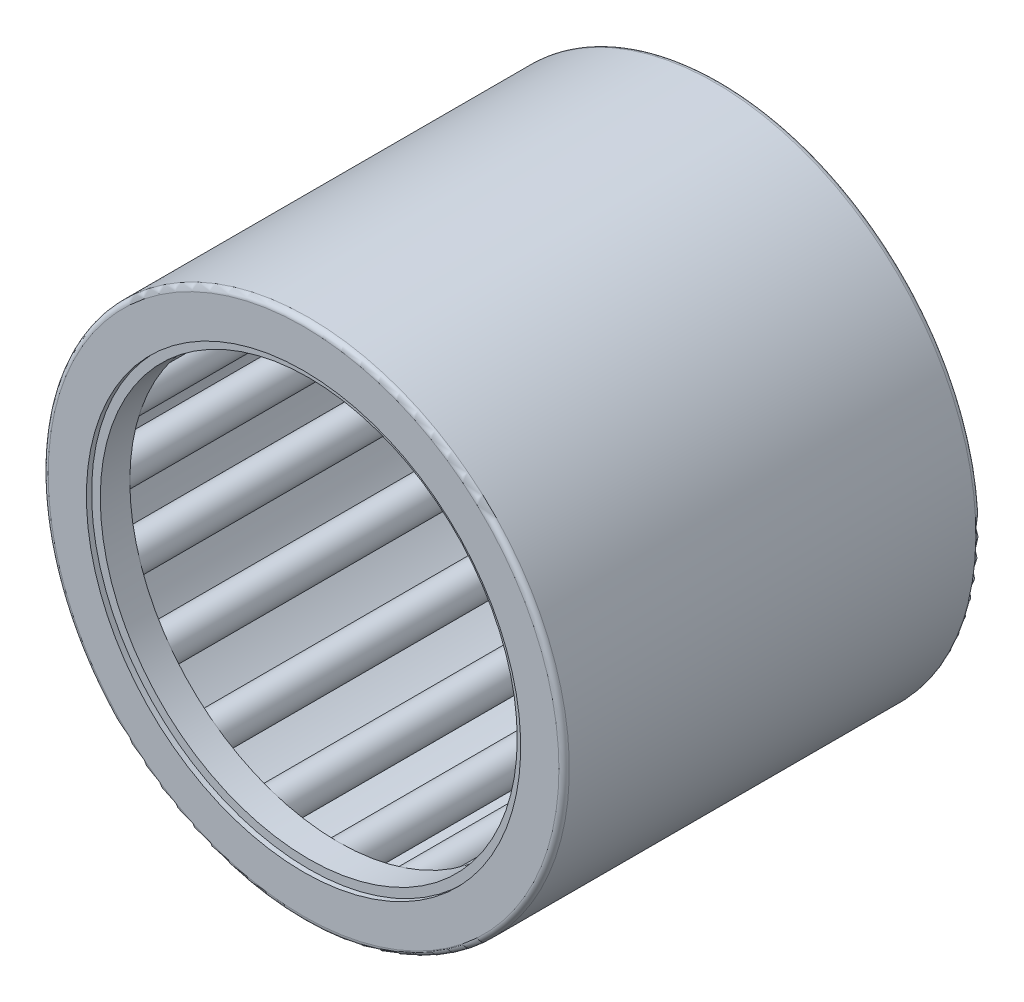
SolidWorks part; units mm, degrees
material "Cast Alloy Steel"
ref_plane "Front Plane" through (0, 0, 0) normal (0, 0, 1) x (1, 0, 0)
ref_plane "Top Plane" through (0, 0, 0) normal (0, 1, 0) x (1, 0, 0)
ref_plane "Right Plane" through (0, 0, 0) normal (1, 0, 0) x (0, 0, -1)
sketch "Sketch1" plane through (0, 0, 0) normal (1, 0, 0) x (0, 0, -1)
  line L0 (-12.7, 0) -> (12.7, 0) construction
  line L1 (0, 0) -> (0, 15.875) construction
  line L2 (-12.7, 0) -> (-12.7, 15.875) construction
  line L3 (-12.7, 15.875) -> (12.7, 15.875)
  line L4 (12.7, 15.875) -> (12.7, 0) construction
  line L5 (12.7, 0) -> (11.6417, 0) construction
  line L6 (11.6417, 0) -> (11.6417, 14.8167) construction
  line L7 (11.6417, 14.8167) -> (-11.6417, 14.8167)
  line L8 (-11.6417, 14.8167) -> (-11.6417, 0) construction
  line L9 (-11.6417, 0) -> (-12.7, 0) construction
  line L10 (-12.7, 15.875) -> (-12.7, 13.2292)
  line L11 (-12.7, 13.2292) -> (-11.6417, 13.2292)
  line L12 (-11.6417, 13.2292) -> (-11.6417, 14.8167)
  line L13 (11.6417, 15.875) -> (11.6417, 14.8167) construction
  line L14 (11.6417, 14.8167) -> (11.6417, 13.2292)
  line L15 (11.6417, 13.2292) -> (12.7, 13.2292)
  line L16 (12.7, 13.2292) -> (12.7, 15.875)
  line L17 (11.6417, 14.8167) -> (11.6417, 13.7583) construction
  line L18 (11.6417, 13.7583) -> (11.6417, 12.7) construction
  line L19 (11.6417, -14.8167) -> (11.6417, -13.7583) construction
  line L20 (11.6417, -15.875) -> (11.6417, -14.8167) construction
  line L21 (12.7, -13.2292) -> (12.7, -15.875) construction
  line L22 (11.6417, -13.2292) -> (12.7, -13.2292) construction
  line L23 (11.6417, -14.8167) -> (11.6417, -13.2292) construction
  line L24 (-11.6417, -13.2292) -> (-11.6417, -14.8167) construction
  line L25 (-12.7, -13.2292) -> (-11.6417, -13.2292) construction
  line L26 (-12.7, -15.875) -> (-12.7, -13.2292) construction
  line L27 (11.6417, -14.8167) -> (-11.6417, -14.8167) construction
  line L28 (-12.7, -15.875) -> (12.7, -15.875) construction
  point P5 (0, 12.7)
  dimension "Width" = 25.4
  dimension "OD" = 31.75
  dimension "Shaft Dia" = 25.4
revolve "Revolve1" add sketch "Sketch1" angle 360 about L0
sketch "Sketch2" plane through (0, 0, 0) normal (1, 0, 0) x (0, 0, -1)
  line L0 (11.6417, 14.8167) -> (-11.6417, 14.8167) construction
  line L1 (-10.5833, 13.7583) -> (10.5833, 13.7583) construction
  line L2 (-10.5833, 13.7583) -> (-10.5833, 14.8167) construction
  line L3 (-10.5833, 14.8167) -> (10.5833, 14.8167)
  line L4 (10.5833, 13.7583) -> (10.5833, 14.8167) construction
  line L5 (11.6417, 13.2292) -> (12.7, 13.2292) construction
  line L6 (-11.6417, 13.7583) -> (-10.5833, 13.7583) construction
  line L7 (10.5833, 13.7583) -> (11.6417, 13.7583) construction
  line L8 (-12.7, 13.2292) -> (-11.6417, 13.2292) construction
  line L9 (-10.5833, 14.0229) -> (-10.5833, 13.4937) construction
  line L10 (-11.6417, 13.7583) -> (-11.6417, 13.2292) construction
  line L11 (-10.5833, 14.8167) -> (-10.5833, 14.0229)
  line L12 (10.5833, 14.8167) -> (10.5833, 14.0229)
  line L13 (10.5833, 14.0229) -> (-10.5833, 14.0229)
  line L14 (0, 14.8167) -> (0, 12.7) construction
  line L15 (-11.6417, 13.2292) -> (-11.6417, 14.8167) construction
  line L16 (-10.5833, 13.4937) -> (-11.6417, 13.4937) construction
  line L17 (0, 0) -> (12.7, 0) construction
  line L18 (-10.5833, -13.4937) -> (-11.6417, -13.4937) construction
  line L19 (0, -14.8167) -> (0, -12.7) construction
  line L20 (-11.6417, -13.7583) -> (-11.6417, -13.2292) construction
  line L21 (-10.5833, -14.0229) -> (-10.5833, -13.4937) construction
  line L22 (10.5833, -13.7583) -> (11.6417, -13.7583) construction
  line L23 (-11.6417, -13.7583) -> (-10.5833, -13.7583) construction
  line L24 (10.5833, -13.7583) -> (10.5833, -14.8167) construction
  line L25 (-10.5833, -13.7583) -> (-10.5833, -14.8167) construction
  line L26 (-10.5833, -13.7583) -> (10.5833, -13.7583) construction
  line L27 (10.5833, -14.0229) -> (-10.5833, -14.0229) construction
  line L28 (10.5833, -14.8167) -> (10.5833, -14.0229) construction
  line L29 (-10.5833, -14.8167) -> (-10.5833, -14.0229) construction
  line L30 (-10.5833, -14.8167) -> (10.5833, -14.8167) construction
  line L31 (12.7, -15.875) -> (12.7, 15.875) construction
  point P16 (0, 13.7583)
revolve "Revolve2" add sketch "Sketch2" angle 360 about L1
sketch "Sketch3" plane through (0, 0, 0) normal (1, 0, 0) x (0, 0, -1)
  line L0 (11.6417, 14.8167) -> (11.6417, 13.2292) construction
  line L1 (-11.6417, 13.7583) -> (11.6417, 13.7583)
  line L2 (-11.6417, 13.7583) -> (-11.6417, 14.0229)
  line L3 (-11.6417, 14.0229) -> (11.6417, 14.0229)
  line L4 (11.6417, 13.7583) -> (11.6417, 14.0229)
  line L5 (0, 0) -> (12.7, 0) construction
  line L6 (12.7, -15.875) -> (12.7, 15.875) construction
  line L7 (11.6417, -13.7583) -> (11.6417, -14.0229) construction
  line L8 (-11.6417, -14.0229) -> (11.6417, -14.0229) construction
  line L9 (-11.6417, -13.7583) -> (-11.6417, -14.0229) construction
  line L10 (-11.6417, -13.7583) -> (11.6417, -13.7583) construction
revolve "Revolve3" add sketch "Sketch3" angle 360 about L1
ref_axis "Axis1" through (0, 0, -12.7) along (0, 0, 1)
pattern_circular "CirPattern1" count 20 every 18 about axis through (0, 0, -12.7) along (0, 0, 1) of bodies 166 167
fillet "Fillet1" radius 0.3175 2 edges at (0, -15.875, -12.7) (0, -15.875, 12.7)
sketch "Sketch4" plane through (0, 0, 0) normal (1, 0, 0) x (0, 0, -1)
  line L1 (12.3825, 12.7) -> (10.5833, 12.7)
  line L2 (12.3825, 12.7) -> (12.3825, 13.2292)
  line L3 (12.3825, 13.2292) -> (10.5833, 13.2292)
  line L4 (10.5833, 12.7) -> (10.5833, 13.2292)
  line L5 (-12.7, 13.2292) -> (-11.6417, 13.2292) construction
  line L6 (12.3825, -15.875) -> (12.3825, 15.875) construction
  line L7 (10.5833, 14.8167) -> (10.5833, 14.0229) construction
revolve "Revolve4" add sketch "Sketch4" angle 360 about L0
sketch "Sketch5" plane through (0, 0, 0) normal (1, 0, 0) x (0, 0, -1)
  line L0 (-12.3825, 15.875) -> (-12.3825, -15.875) construction
  line L1 (-10.5833, 12.7) -> (-12.3825, 12.7)
  line L2 (-10.5833, 12.7) -> (-10.5833, 13.2292)
  line L3 (-10.5833, 13.2292) -> (-12.3825, 13.2292)
  line L4 (-12.3825, 12.7) -> (-12.3825, 13.2292)
  line L6 (-10.5833, 14.8167) -> (-10.5833, 14.0229) construction
  line L7 (-12.7, 13.2292) -> (-11.6417, 13.2292) construction
revolve "Revolve5" add sketch "Sketch5" angle 360 about L0
equation "\"Angle@CirPattern1\" = 360/\"Rollers@CirPattern1\""
equation "\"Rollers@CirPattern1\" = \"OD@Sketch1\"*16"
equation "\"D1@Fillet1\" = \"OD@Sketch1\"*.01"
